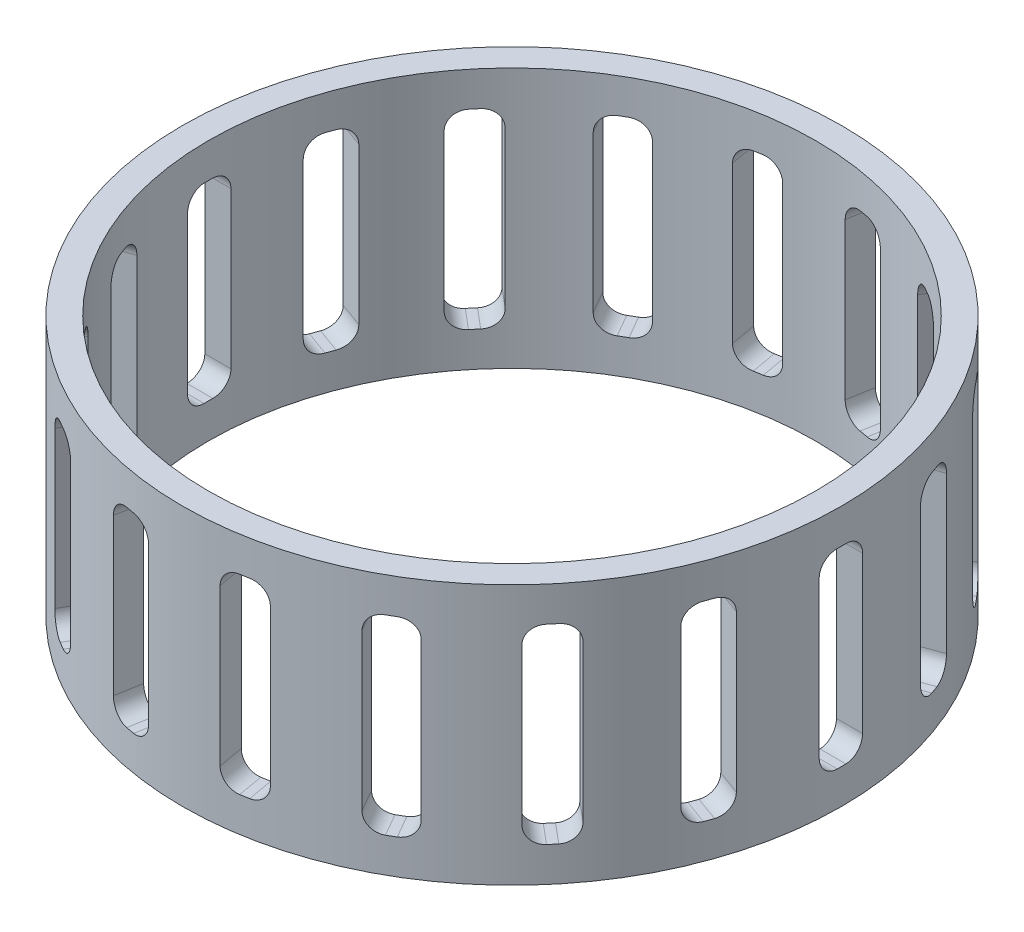
SolidWorks part; units mm, degrees
material "6061-T6 (SS)"
ref_plane "Płaszczyzna przednia" through (0, 0, 0) normal (0, 0, 1) x (1, 0, 0)
ref_plane "Płaszczyzna górna" through (0, 0, 0) normal (0, 1, 0) x (1, 0, 0)
ref_plane "Płaszczyzna prawa" through (0, 0, 0) normal (1, 0, 0) x (0, 0, -1)
sketch "Szkic1" plane through (0, 0, 0) normal (0, 0, 1) x (1, 0, 0)
  line L0 (0, -11.5417) -> (0, 16.5417) construction
  line L1 (-38, 15) -> (-38, -15)
  line L2 (-38, -15) -> (-35, -15)
  line L3 (-35, -15) -> (-35, 15)
  line L4 (-35, 15) -> (-38, 15)
  point P5 (-38, 0)
  dimension "D1" = 3
  dimension "D2" = 70
  dimension "D3" = 30
revolve "Obrót1" add sketch "Szkic1" angle 360 about L0
sketch "Szkic2" plane through (0, 0, 0) normal (1, 0, 0) x (0, 0, -1)
  line L0 (35, 15) -> (-35, 15) construction
  line L1 (38, 15) -> (-38, 15) construction
  line L2 (-38, -15) -> (38, -15) construction
  line L3 (-35, -15) -> (35, -15) construction
  line L4 (35, 15) -> (-35, 15)
  line L5 (38, 15) -> (-38, 15)
  line L6 (-38, -15) -> (38, -15)
  line L7 (-35, -15) -> (35, -15)
  line L8 (0, 15) -> (0, -15) construction
  line L9 (2.5, 11) -> (-2.5, 11)
  line L10 (-2.5, 11) -> (-2.5, -11)
  line L11 (-2.5, -11) -> (2.5, -11)
  line L12 (2.5, -11) -> (2.5, 11)
  point P12 (-2.5, 0)
  point P15 (0, 11)
  dimension "D1" = 5
  dimension "D2" = 4
extrude "Wytnij-wyciągnięcie1" cut sketch "Szkic2" against normal up to surface (37.9177 mm away) contours L8 L9 L10 L11 | L9 L8 L11 L12
fillet "Zaokrąglenie1" radius 2 4 edges at (-36.4141, -11, -2.5) (-36.4141, -11, 2.5) (-36.4141, 11, -2.5) (-36.4141, 11, 2.5)
pattern_circular "Szyk kołowy1" count 18 over 360 about axis through (0, 0, 0) along (0, 1, 0) of "Wytnij-wyciągnięcie1", "Zaokrąglenie1"
